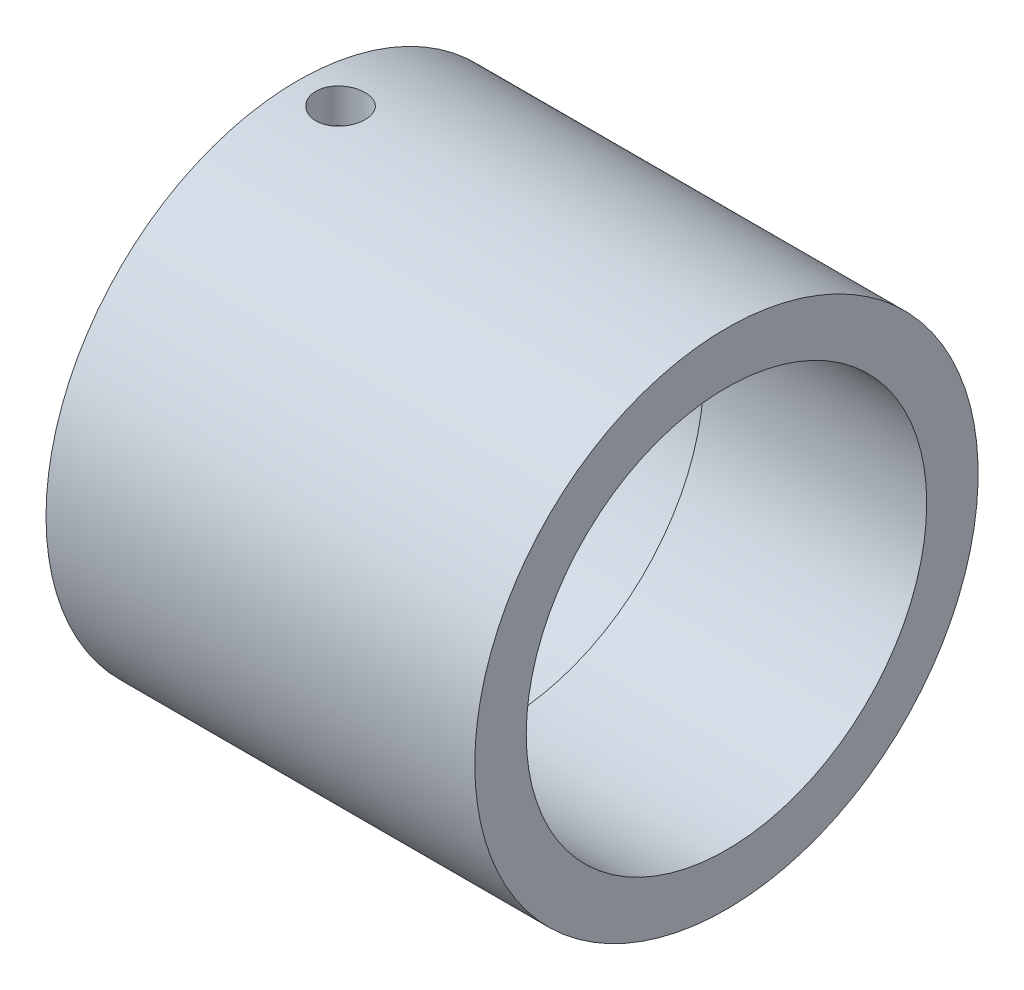
SolidWorks part; units mm, degrees
ref_plane "Alzado" through (0, 0, 0) normal (0, 0, 1) x (1, 0, 0)
ref_plane "Planta" through (0, 0, 0) normal (0, 1, 0) x (1, 0, 0)
ref_plane "Vista lateral" through (0, 0, 0) normal (1, 0, 0) x (0, 0, -1)
sketch "Croquis3" plane through (0, 0, 0) normal (0, 1, 0) x (1, 0, 0)
  line L0 (-30.3674, 0) -> (30.3674, 0) construction
  line L1 (0, 11.675) -> (-13, 11.675)
  line L2 (-13, 11.675) -> (-13, 12.675)
  line L3 (-13, 12.675) -> (-25, 12.675)
  line L4 (-25, 12.675) -> (-25, 14.675)
  line L5 (-25, 14.675) -> (0, 14.675)
  line L6 (0, 14.675) -> (0, 11.675)
  point P3 (0, 0)
  point P6 (-25, 13.675)
  dimension "D1" = 29.35
  dimension "D2" = 23.35
  dimension "D3" = 2
  dimension "D4" = 25
  dimension "D5" = 12
revolve "Revolución1" add sketch "Croquis3" angle 360 about L0
sketch "Croquis4" plane through (0, 0, 0) normal (0, 1, 0) x (1, 0, 0)
  line L0 (-25, 14.675) -> (-25, -14.675) construction
  circle A0 centre (-22.5, 0) radius 1.435
  dimension "D1" = 2.87
  dimension "D2" = 2.5
extrude "Cortar-Extruir1" cut sketch "Croquis4" against normal through all both and the other way through all contours A0
